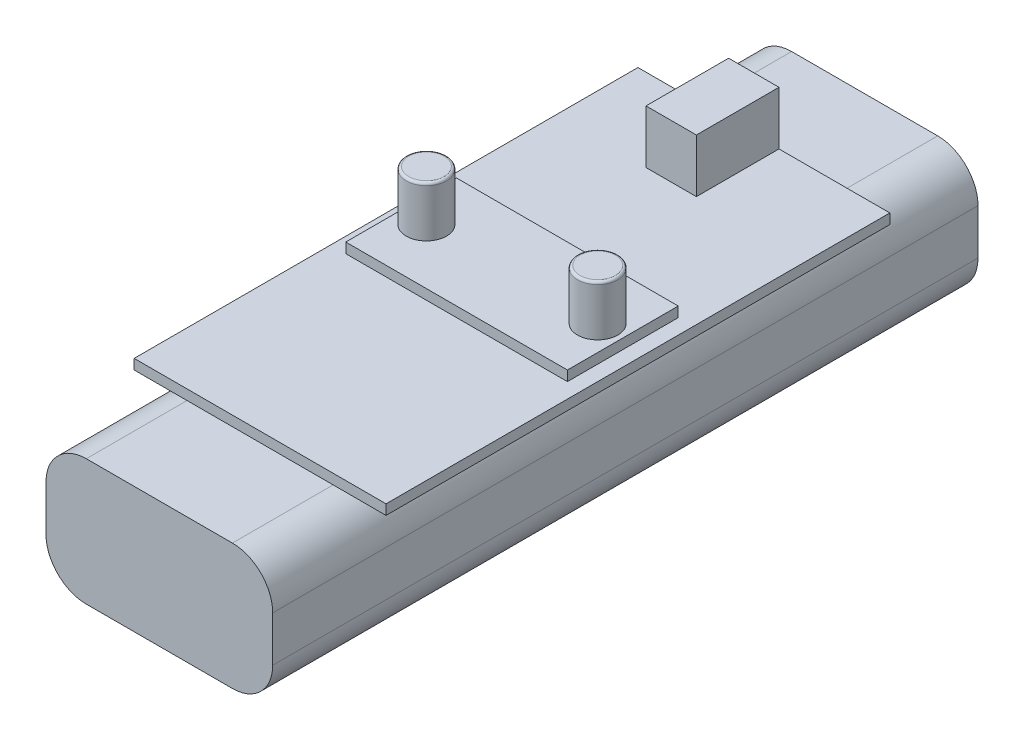
SolidWorks part; units mm, degrees
ref_plane "Front" through (0, 0, 0) normal (0, 0, 1) x (1, 0, 0)
ref_plane "Top" through (0, 0, 0) normal (0, 1, 0) x (1, 0, 0)
ref_plane "Right" through (0, 0, 0) normal (1, 0, 0) x (0, 0, -1)
sketch "Skizze1" plane through (0, 0, 0) normal (0, 1, 0) x (1, 0, 0)
  line L1 (-22.5, -70) -> (22.5, -70)
  line L2 (-22.5, -70) -> (-22.5, 70)
  line L3 (-22.5, 70) -> (22.5, 70)
  line L4 (22.5, -70) -> (22.5, 70)
  line L5 (-22.5, -70) -> (22.5, 70) construction
  line L6 (-22.5, 70) -> (22.5, -70) construction
  point P1 (0, 0)
  dimension "D1" = 140
  dimension "D2" = 45
extrude "Aufsatz-Linear austragen1" add sketch "Skizze1" along normal blind 25
fillet "Verrundung1" radius 8 4 edges at (-22.5, 25, 0) (-22.5, 0, 0) (22.5, 25, 0) (22.5, 0, 0)
sketch "Skizze2" plane through (0, 25, 0) normal (0, 1, 0) x (1, 0, 0)
  line L1 (25, -50) -> (-25, -50)
  line L2 (25, -50) -> (25, 50)
  line L3 (25, 50) -> (-25, 50)
  line L4 (-25, -50) -> (-25, 50)
  line L5 (25, -50) -> (-25, 50) construction
  line L6 (25, 50) -> (-25, -50) construction
  point P0 (0, 0)
  dimension "D1" = 100
  dimension "D2" = 50
extrude "Aufsatz-Linear austragen2" add sketch "Skizze2" along normal blind 2
ref_plane "Ebene1" through (-25, 27, -50) normal (-1, 0, 0) x (0, 0, 1)
sketch "Skizze4" plane through (0, 27, 0) normal (0, 1, 0) x (1, 0, 0)
  line L0 (25, 50) -> (-25, 50) construction
  line L1 (-7, 50) -> (3, 50)
  line L2 (-7, 50) -> (-7, 33.6)
  line L3 (-7, 33.6) -> (3, 33.6)
  line L4 (3, 50) -> (3, 33.6)
  line L5 (25, -50) -> (25, 50) construction
  line L6 (-25, 50) -> (-25, -50) construction
  point P6 (3, 41.8)
  dimension "D1" = 10
  dimension "D2" = 16.4
  dimension "D3" = 16.4
  dimension "D4" = 22
  dimension "D5" = 18
extrude "Aufsatz-Linear austragen3" add sketch "Skizze4" along normal blind 10.6
sketch "Skizze5" plane through (0, 27, 0) normal (0, 1, 0) x (1, 0, 0)
  line L0 (-25, 50) -> (-25, -50) construction
  line L1 (-22, -11) -> (22, -11)
  line L2 (-22, -11) -> (-22, 11)
  line L3 (-22, 11) -> (22, 11)
  line L4 (22, -11) -> (22, 11)
  line L5 (-22, -11) -> (22, 11) construction
  line L6 (-22, 11) -> (22, -11) construction
  point P0 (0, 0)
  point P6 (-22, 0)
  dimension "D1" = 22
  dimension "D2" = 44
  dimension "D3" = 3
extrude "Aufsatz-Linear austragen4" add sketch "Skizze5" along normal blind 2 separate body
sketch "Skizze6" plane through (0, 29, 0) normal (0, 1, 0) x (1, 0, 0)
  line L0 (22, -11) -> (22, 11) construction
  line L1 (-22, 11) -> (-22, -11) construction
  circle A0 centre (17, 0) radius 4
  circle A1 centre (-17, 0.0136) radius 4
  dimension "D1" = 8
  dimension "D2" = 5
  dimension "D3" = 5
extrude "Aufsatz-Linear austragen5" add sketch "Skizze6" along normal blind 10
fillet "Verrundung2" radius 0.5 2 edges at (17, 39, 4) (-17, 39, 3.9864)
